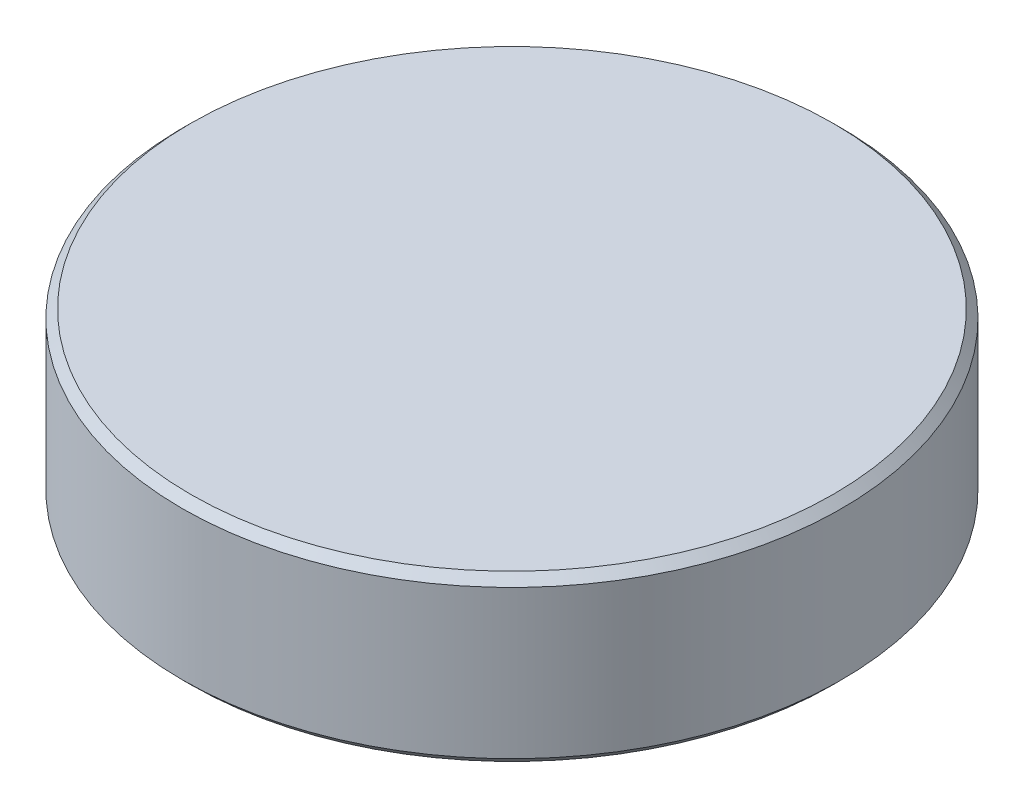
SolidWorks part; units mm, degrees
ref_plane "Face" through (0, 0, 0) normal (0, 0, 1) x (1, 0, 0)
ref_plane "Dessus" through (0, 0, 0) normal (0, 1, 0) x (1, 0, 0)
ref_plane "Droite" through (0, 0, 0) normal (1, 0, 0) x (0, 0, -1)
sketch "Esquisse1" plane through (0, 0, 0) normal (0, 1, 0) x (1, 0, 0)
  circle A0 centre (0, 0) radius 100
  dimension "D1" = 200
extrude "Extrusion1" add sketch "Esquisse1" along normal blind 50
chamfer "Chanfrein1" distance 2.5 angle 45 2 edges at (0, 0, 100) (0, 50, 100)
